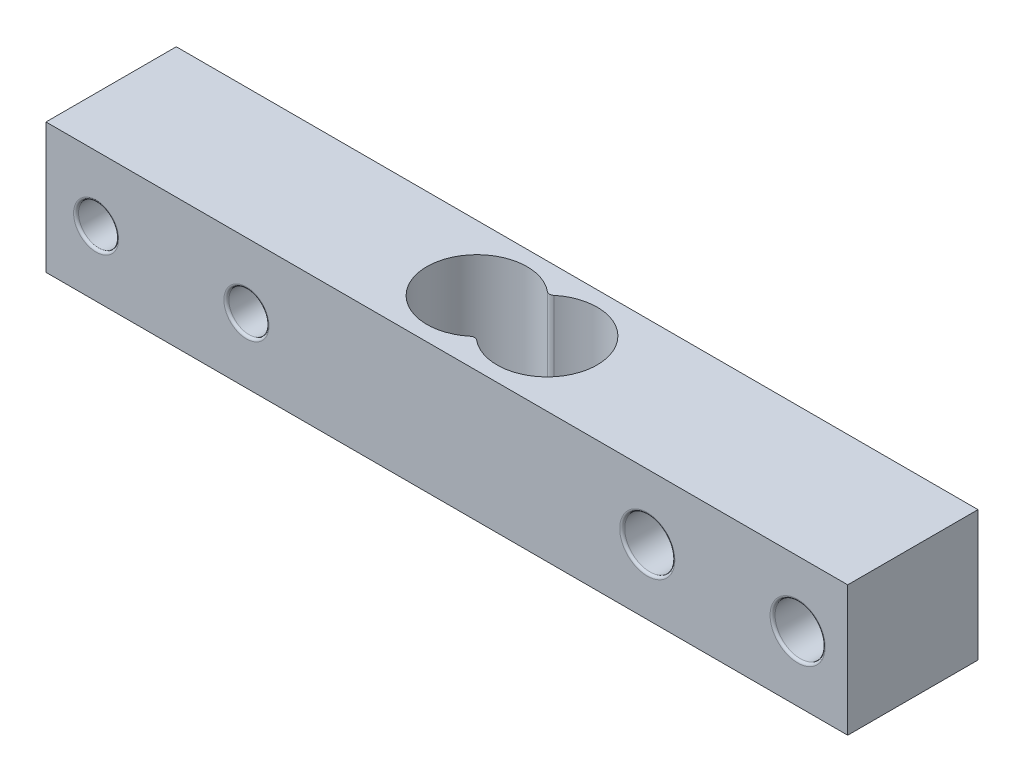
SolidWorks part; units mm, degrees
ref_plane "Front Plane" through (0, 0, 0) normal (0, 0, 1) x (1, 0, 0)
ref_plane "Top Plane" through (0, 0, 0) normal (0, 1, 0) x (1, 0, 0)
ref_plane "Right Plane" through (0, 0, 0) normal (1, 0, 0) x (0, 0, -1)
ref_plane "Plane1" through (0, 0, 0) normal (0, -1, 0) x (1, 0, 0)
sketch "Sketch1" plane through (0, 0, 0) normal (0, -1, 0) x (1, 0, 0)
  line L0 (52.0209, -0.5539) -> (-27.9791, -0.5539)
  line L1 (-27.9791, -0.5539) -> (-27.9791, -13.5539)
  line L2 (-27.9791, -13.5539) -> (52.0209, -13.5539)
  line L3 (52.0209, -13.5539) -> (52.0209, -0.5539)
extrude "Boss-Extrude1" add sketch "Sketch1" against normal blind 13
hole_wizard "Ø5.0 (5) Diameter Hole1" positions "Sketch3" profile "Sketch2" hole size "Ø5.0" standard "ANSI Metric"
sketch "Sketch3" plane through (0, 0, -0.5539) normal (0, 0, 1) x (1, 0, 0)
  point P0 (32.0209, 6.5)
  point P1 (47.0209, 6.5)
sketch "Sketch2" plane through (32.0209, 6.5, -0.5539) normal (1, 0, 0) x (0, -1, 0)
  line L0 (0, 0) -> (0, 13)
  line L1 (0, 13) -> (2.5, 13)
  line L2 (2.5, 13) -> (2.5, 0)
  line L5 (2.5, 0) -> (0, 0)
  line L11 (0, -6.35) -> (0, 107.95) construction
  dimension "Thru Hole Dia." = 5
  dimension "Thru Hole Depth" = 13
hole_wizard "Ø4.0 (4) Diameter Hole1" positions "Sketch5" profile "Sketch4" hole size "Ø4.0" standard "ANSI Metric"
sketch "Sketch5" plane through (0, 0, -0.5539) normal (0, 0, 1) x (1, 0, 0)
  point P0 (-7.9791, 6.5)
sketch "Sketch4" plane through (-7.9791, 6.5, -0.5539) normal (1, 0, 0) x (0, -1, 0)
  line L0 (0, 0) -> (0, 13)
  line L1 (0, 13) -> (2, 13)
  line L2 (2, 13) -> (2, 0)
  line L5 (2, 0) -> (0, 0)
  line L11 (0, -6.35) -> (0, 107.95) construction
  dimension "Thru Hole Dia." = 4
  dimension "Thru Hole Depth" = 13
hole_wizard "Ø4.0 (4) Diameter Hole2" positions "Sketch7" profile "Sketch6" hole size "Ø4.0" standard "ANSI Metric"
sketch "Sketch7" plane through (0, 0, -13.5539) normal (0, 0, -1) x (-1, 0, 0)
  point P0 (22.9791, 6.5)
sketch "Sketch6" plane through (-22.9791, 6.5, -13.5539) normal (1, 0, 0) x (0, 1, 0)
  line L0 (0, 0) -> (0, 13)
  line L1 (0, 13) -> (2, 13)
  line L2 (2, 13) -> (2, 0)
  line L5 (2, 0) -> (0, 0)
  line L11 (0, -6.35) -> (0, 107.95) construction
  dimension "Thru Hole Dia." = 4
  dimension "Thru Hole Depth" = 13
hole_wizard "Ø10.0 (10) Diameter Hole1" positions "Sketch9" profile "Sketch8" hole size "Ø10.0" standard "ANSI Metric"
sketch "Sketch9" plane through (0, 13, 0) normal (0, 1, 0) x (1, 0, 0)
  point P0 (8.5209, 7.0539)
sketch "Sketch8" plane through (8.5209, 13, -7.0539) normal (1, 0, 0) x (0, 0, 1)
  line L0 (0, 0) -> (0, 13)
  line L1 (0, 13) -> (5, 13)
  line L2 (5, 13) -> (5, 0)
  line L5 (5, 0) -> (0, 0)
  line L11 (0, -6.35) -> (0, 107.95) construction
  dimension "Thru Hole Dia." = 10
  dimension "Thru Hole Depth" = 13
hole_wizard "Ø10.0 (10) Diameter Hole2" positions "Sketch11" profile "Sketch10" hole size "Ø10.0" standard "ANSI Metric"
sketch "Sketch11" plane through (0, 0, 0) normal (0, -1, 0) x (-1, 0, 0)
  point P0 (-15.5209, 7.0539)
sketch "Sketch10" plane through (15.5209, 0, -7.0539) normal (1, 0, 0) x (0, 0, -1)
  line L0 (0, 0) -> (0, 13)
  line L1 (0, 13) -> (5, 13)
  line L2 (5, 13) -> (5, 0)
  line L5 (5, 0) -> (0, 0)
  line L11 (0, -6.35) -> (0, 107.95) construction
  dimension "Thru Hole Dia." = 10
  dimension "Thru Hole Depth" = 13
fillet "Fillet1" radius 0.25 8 edges at (-5.9791, 6.5, -13.5539) (-5.9791, 6.5, -0.5539) (34.5209, 6.5, -13.5539) (49.5209, 6.5, -13.5539) (34.5209, 6.5, -0.5539) (-24.9791, 6.5, -0.5539) (49.5209, 6.5, -0.5539) (-24.9791, 6.5, -13.5539)
fillet "Fillet2" radius 0.5 2 edges at (12.0209, 6.5, -10.6246) (12.0209, 6.5, -3.4831)
